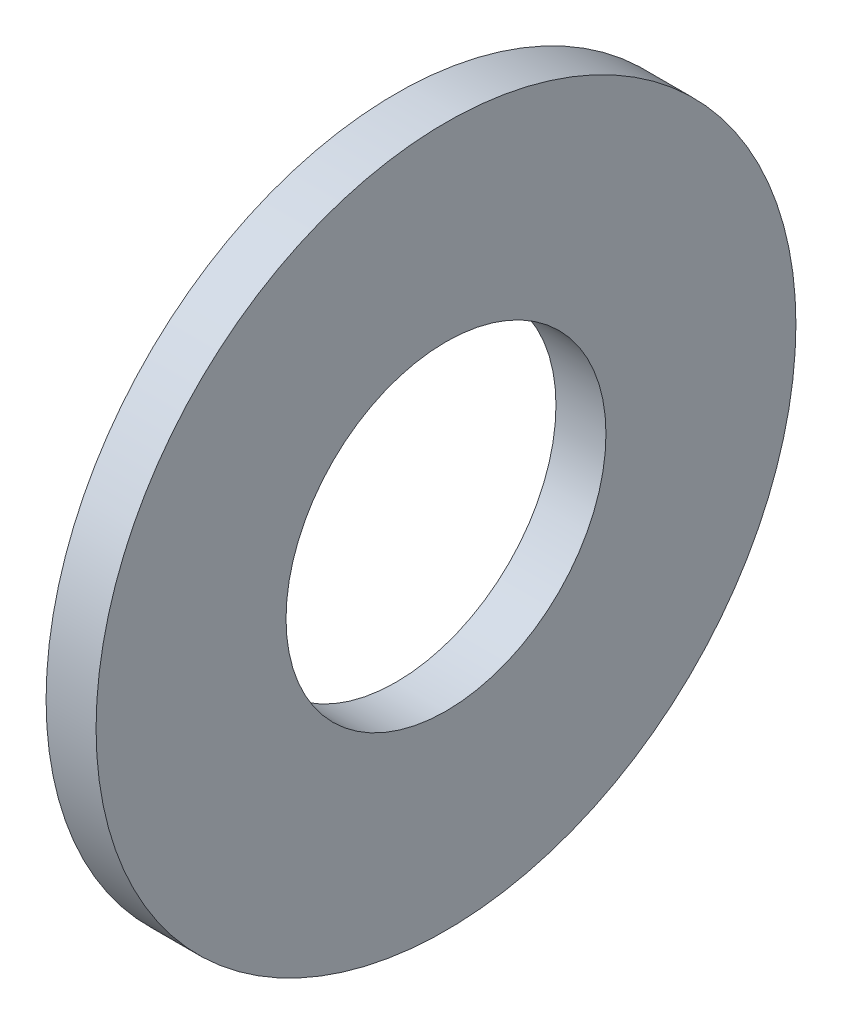
SolidWorks part; units mm, degrees
ref_plane "Plane1" through (0, 0, 0) normal (0, 0, 1) x (1, 0, 0)
ref_plane "Plane2" through (0, 0, 0) normal (0, 1, 0) x (1, 0, 0)
ref_plane "Plane3" through (0, 0, 0) normal (1, 0, 0) x (0, 0, -1)
sketch "Sketch1" plane through (0, 0, 0) normal (0, 0, 1) x (1, 0, 0)
  line L0 (-34.925, 0) -> (9.525, 0) construction
  line L1 (0, 1.6) -> (0, 3.5)
  line L2 (0, 3.5) -> (-0.5, 3.5)
  line L3 (-0.5, 3.5) -> (-0.5, 1.6)
  line L4 (-0.5, 1.6) -> (0, 1.6)
  dimension "Thickness" = 0.5
  dimension "Inside_dia" = 3.2
  dimension "Outside_dia" = 7
revolve "Base-Revolve" add sketch "Sketch1" angle 360 about L0
chamfer "ODChamfer" [suppressed] distance 0.125 angle 45
equation "\"D1@ODChamfer\" =  \"Thickness@Sketch1\" * 0.25"
